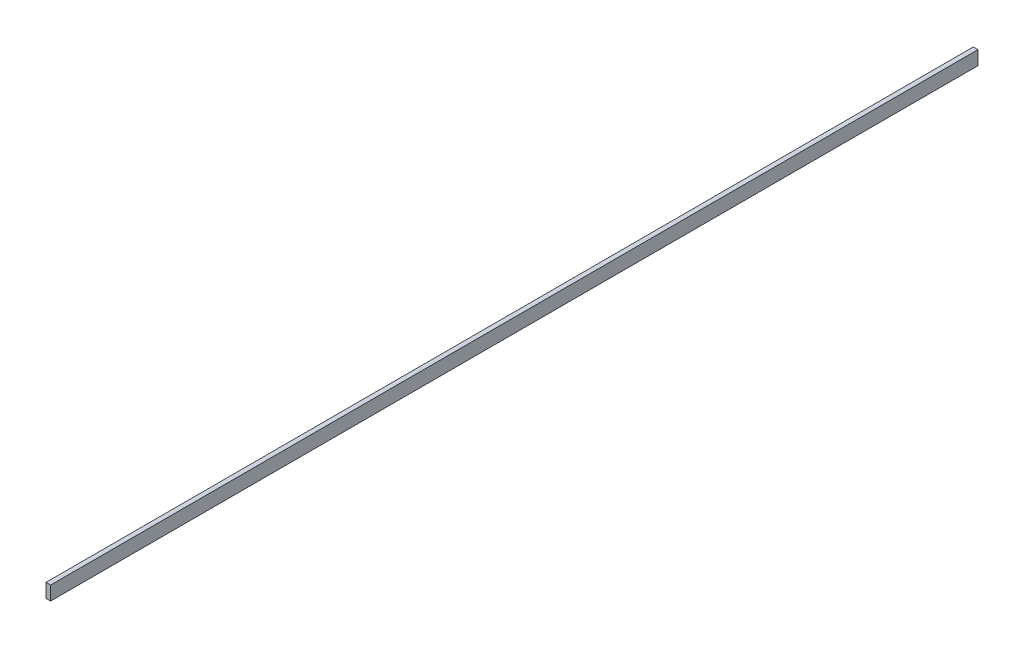
SolidWorks part; units mm, degrees
ref_plane "Plano frontal" through (0, 0, 0) normal (0, 0, 1) x (1, 0, 0)
ref_plane "Plano superior" through (0, 0, 0) normal (0, 1, 0) x (1, 0, 0)
ref_plane "Plano direito" through (0, 0, 0) normal (1, 0, 0) x (0, 0, -1)
sketch "Esboço1" plane through (0, 0, 0) normal (0, 0, 1) x (1, 0, 0)
  line L1 (-1, 3) -> (1, 3)
  line L2 (-1, 3) -> (-1, -3)
  line L3 (-1, -3) -> (1, -3)
  line L4 (1, 3) -> (1, -3)
  line L5 (-1, 3) -> (1, -3) construction
  line L6 (-1, -3) -> (1, 3) construction
  point P0 (0, 0)
  dimension "D1" = 2
  dimension "D2" = 6
sketch "Esboço2" plane through (0, 0, 0) normal (0, 1, 0) x (1, 0, 0)
  line L0 (0, 0) -> (0, 400)
  dimension "D1" = 400
sweep "Varredura1" add profiles "Esboço1" path "Esboço2"
